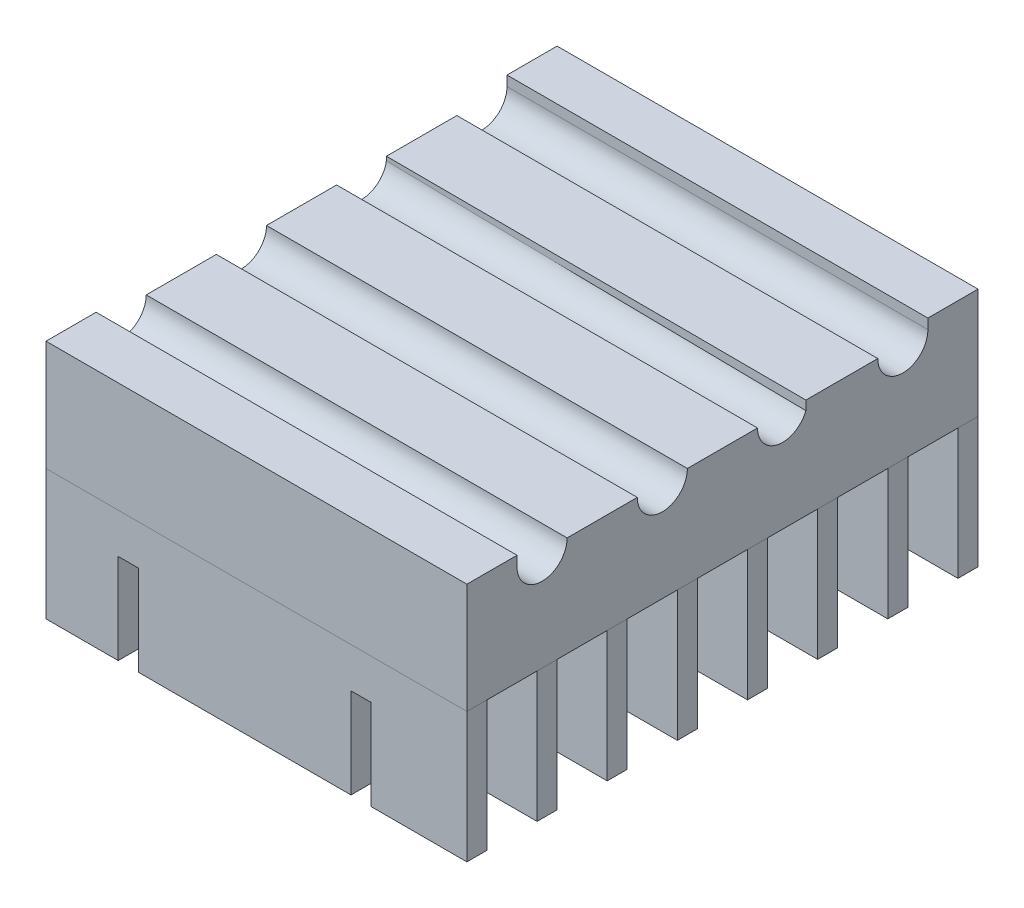
SolidWorks part; units mm, degrees
ref_plane "Front Plane" through (0, 0, 0) normal (0, 0, 1) x (1, 0, 0)
ref_plane "Top Plane" through (0, 0, 0) normal (0, 1, 0) x (1, 0, 0)
ref_plane "Right Plane" through (0, 0, 0) normal (1, 0, 0) x (0, 0, -1)
sketch "Sketch2" plane through (0, 0, 0) normal (0, 1, 0) x (1, 0, 0)
  line L0 (-19.8197, 1.623) -> (-19.8197, -5.377)
  line L1 (22.1803, 1.623) -> (22.1803, -5.377)
  line L2 (-28.8197, 6.623) -> (-28.8026, 6.623)
  line L3 (-19.8197, 6.5922) -> (22.1803, 6.4481)
  line L4 (-19.8197, 1.623) -> (22.1803, 1.623)
  line L5 (-19.8197, -5.377) -> (22.1803, -5.377)
  line L6 (-19.8197, -10.377) -> (22.1803, -10.377)
  line L7 (-19.8197, -10.377) -> (-19.8197, -17.377)
  line L8 (-19.8197, -17.377) -> (22.1803, -17.377)
  line L9 (-19.8197, 13.623) -> (-19.8197, 6.5922)
  line L11 (22.1803, 13.623) -> (22.1803, 6.4481)
  line L12 (22.1803, -10.377) -> (22.1803, -17.377)
  line L21 (-19.8197, 13.623) -> (22.1803, 13.623)
  arc A5 (-28.8026, 6.623) -> (-28.8197, 6.623) centre (-28.8197, 4.123) ccw
  point P0 (1.1803, -1.377)
extrude "Boss-Extrude1" add sketch "Sketch2" along normal blind 10
sketch "Sketch3" plane through (22.1803, 0, 0) normal (1, 0, 0) x (0, 0, -1)
  line L0 (-17.377, 10) -> (-10.377, 10)
  line L1 (-5.377, 10) -> (1.623, 10)
  line L4 (-22.377, 10) -> (-22.377, 11)
  line L5 (-27.377, 11) -> (-27.377, 0)
  line L6 (-27.377, 0) -> (23.623, 0)
  line L7 (-22.377, 11) -> (-27.377, 11)
  line L8 (-5.377, 0) -> (1.623, 0) construction
  line L9 (18.623, 11) -> (23.623, 11)
  line L10 (23.623, 11) -> (23.623, 0)
  line L11 (18.623, 10) -> (18.623, 11)
  line L12 (13.623, 10) -> (6.623, 10)
  arc A0 (-10.377, 10) -> (-5.377, 10) centre (-7.877, 10) ccw
  arc A1 (-22.377, 10) -> (-17.377, 10) centre (-19.877, 10) ccw
  arc A2 (18.623, 10) -> (13.623, 10) centre (16.123, 10) cw
  arc A3 (6.623, 10) -> (1.623, 10) centre (4.123, 10) cw
  point P21 (-1.877, 0)
extrude "Boss-Extrude2" add sketch "Sketch3" against normal up to surface (42 mm away) up to face at (-19.8197, 5, 1.877)
sketch "Sketch4" plane through (22.1803, 0, 0) normal (1, 0, 0) x (0, 0, -1)
  line L0 (23.623, 0) -> (23.623, -13)
  line L1 (23.623, -13) -> (21.623, -13)
  line L2 (21.623, -13) -> (21.623, 0)
  line L3 (-27.377, 0) -> (23.623, 0) construction
  line L4 (21.623, 0) -> (23.623, 0)
extrude "Boss-Extrude3" add sketch "Sketch4" against normal up to surface (42 mm away) separate body contours L0 L1 L2 L4 up to face at (-19.8197, 8.2541, 1.3265)
pattern_linear "LPattern1" count 8 spacing 7 along (0, 0, 1) of "Boss-Extrude3"
sketch "Sketch5" plane through (0, 0, 27.377) normal (0, 0, 1) x (1, 0, 0)
  line L0 (12.6138, -13) -> (12.6138, -4)
  line L1 (-19.8197, -13) -> (22.1803, -13) construction
  line L2 (12.6138, -4) -> (10.6138, -4)
  line L3 (10.6138, -4) -> (10.6138, -14.372)
  line L4 (10.6138, -14.372) -> (12.6138, -14.372)
  line L5 (12.6138, -14.372) -> (12.6138, -13)
  line L7 (-12.6138, -14.372) -> (-12.6138, -13)
  line L8 (-10.6138, -14.372) -> (-12.6138, -14.372)
  line L9 (-10.6138, -4) -> (-10.6138, -14.372)
  line L10 (-12.6138, -4) -> (-10.6138, -4)
  line L11 (-12.6138, -13) -> (-12.6138, -4)
extrude "Cut-Extrude1" cut sketch "Sketch5" against normal up to surface (51 mm away) up to face at (1.1803, -6.5, -23.623)
ref_plane "Plane1" through (1.1803, 0, 0) normal (1, 0, 0) x (0, 0, -1)
